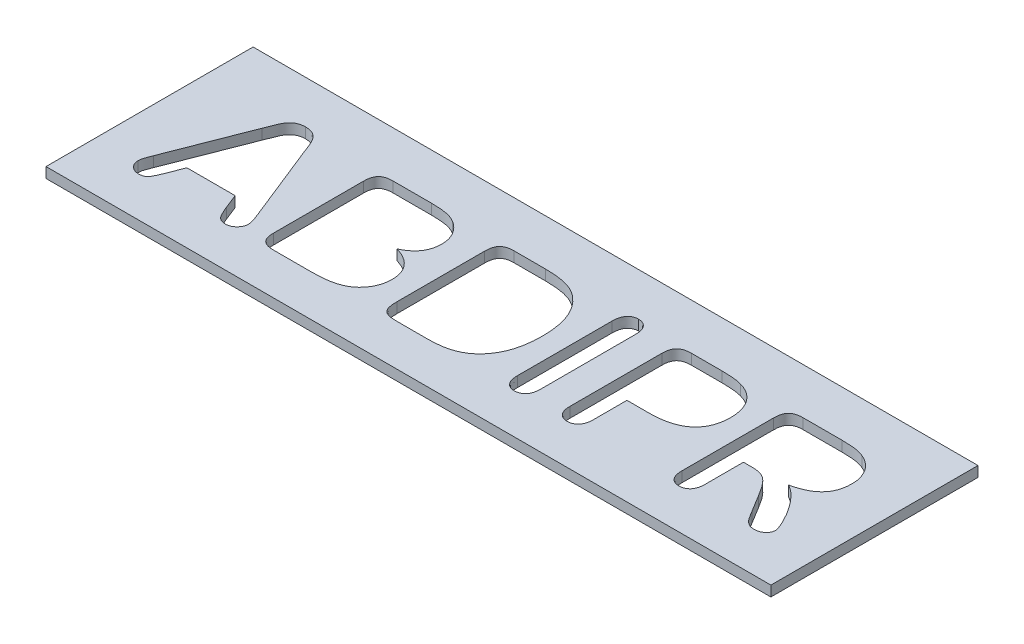
SolidWorks part; units mm, degrees
material "BUTYL"
ref_plane "Front Plane" through (0, 0, 0) normal (0, 0, 1) x (1, 0, 0)
ref_plane "Top Plane" through (0, 0, 0) normal (0, 1, 0) x (1, 0, 0)
ref_plane "Right Plane" through (0, 0, 0) normal (1, 0, 0) x (0, 0, -1)
sketch "Sketch1" plane through (0, 0, 0) normal (0, 1, 0) x (1, 0, 0)
  line L1 (17.5, -5) -> (-17.5, -5)
  line L2 (17.5, -5) -> (17.5, 5)
  line L3 (17.5, 5) -> (-17.5, 5)
  line L4 (-17.5, -5) -> (-17.5, 5)
  line L5 (17.5, -5) -> (-17.5, 5) construction
  line L6 (17.5, 5) -> (-17.5, -5) construction
  point P0 (0, 0)
  dimension "D1" = 35
  dimension "D2" = 10
extrude "Boss-Extrude1" add sketch "Sketch1" along normal blind 0.5
sketch "Sketch3" plane through (0, 0.5, 0) normal (0, 1, 0) x (1, 0, 0)
  line L0 (-17.5, -3) -> (17.5, -3) construction
  line L1 (-17.5, 5) -> (-17.5, -5) construction
  text T0 "ABDIPR" font "Arial Rounded MT Bold" height 6
  point P5 (-17.5, -2.7431)
  dimension "D1" = 35
  dimension "D2" = 3
extrude "Cut-Extrude4" cut sketch "Sketch3" against normal blind 2
